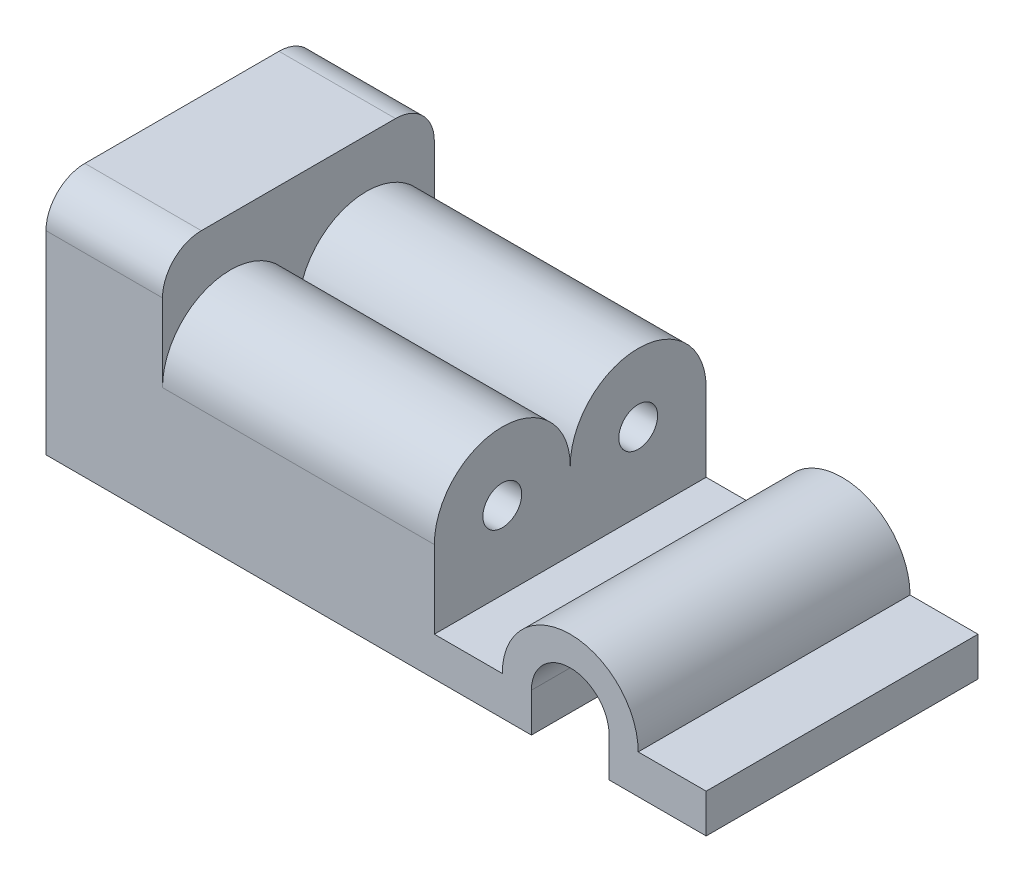
SolidWorks part; units mm, degrees
ref_plane "Front Plane" through (0, 0, 0) normal (0, 0, 1) x (1, 0, 0)
ref_plane "Top Plane" through (0, 0, 0) normal (0, 1, 0) x (1, 0, 0)
ref_plane "Right Plane" through (0, 0, 0) normal (1, 0, 0) x (0, 0, -1)
sketch "Sketch1" plane through (0, 0, 0) normal (0, 0, 1) x (1, 0, 0)
  line L0 (-75.1724, -24.3103) -> (-75.1724, 35.6897)
  line L1 (-75.1724, 35.6897) -> (-45.1724, 35.6897)
  line L2 (-45.1724, 35.6897) -> (-45.1724, 5.6897)
  line L3 (-45.1724, 5.6897) -> (24.8276, 5.6897)
  line L4 (-75.1724, -24.3103) -> (49.8276, -24.3103)
  line L5 (24.8276, 5.6897) -> (24.8276, -14.3103)
  line L6 (24.8276, -14.3103) -> (42.3276, -14.3103)
  line L7 (49.8276, -14.3011) -> (49.8276, -24.3103)
  line L9 (77.3276, -14.3103) -> (94.8276, -14.3103)
  line L10 (94.8276, -14.3103) -> (94.8276, -24.3103)
  line L11 (94.8276, -24.3103) -> (69.8276, -24.3103)
  line L12 (69.8276, -24.3103) -> (69.8276, -14.3011)
  arc A0 (42.3276, -14.3103) -> (77.3276, -14.3103) centre (59.8276, -14.3011) cw
  arc A1 (69.8276, -14.3011) -> (49.8276, -14.3011) centre (59.8276, -14.3011) ccw
  dimension "D6" = 17.5
  dimension "D7" = 10
  dimension "D1" = 60
  dimension "D2" = 30
  dimension "D3" = 125
  dimension "D4" = 10
  dimension "D5" = 30
  dimension "D8" = 35
  dimension "D9" = 10
extrude "Boss-Extrude1" add sketch "Sketch1" along normal mid plane 70
fillet "Fillet1" radius 10 1 edges at (-60.1724, 35.6897, 35)
fillet "Fillet2" radius 10 1 edges at (-60.1724, 35.6897, -35)
sketch "Sketch3" plane through (-45.1724, 0, 0) normal (1, 0, 0) x (0, 0, -1)
  line L0 (0, 42.203) -> (0, -30.8236) construction
  line L1 (-35, 5.6897) -> (35, 5.6897) construction
  line L2 (-35, 5.6897) -> (35, 5.6897)
  arc A0 (0, 5.6897) -> (-35, 5.6897) centre (-17.5, 5.6897) ccw
  arc A1 (35, 5.6897) -> (0, 5.6897) centre (17.5, 5.6897) ccw
  line M6 (-35, 5.6897) -> (35, 5.6897)
  dimension "D1" = 35
extrude "Boss-Extrude2" add sketch "Sketch3" along normal blind 70 contours A0 M6 | L2 A1
sketch "Sketch4" plane through (24.8276, 0, 0) normal (1, 0, 0) x (0, 0, -1)
  circle A0 centre (-17.5, 5.6897) radius 5
  circle A1 centre (17.5, 5.6897) radius 5
  dimension "D1" = 10
  dimension "D2" = 10
extrude "Cut-Extrude1" cut sketch "Sketch4" against normal blind 70
